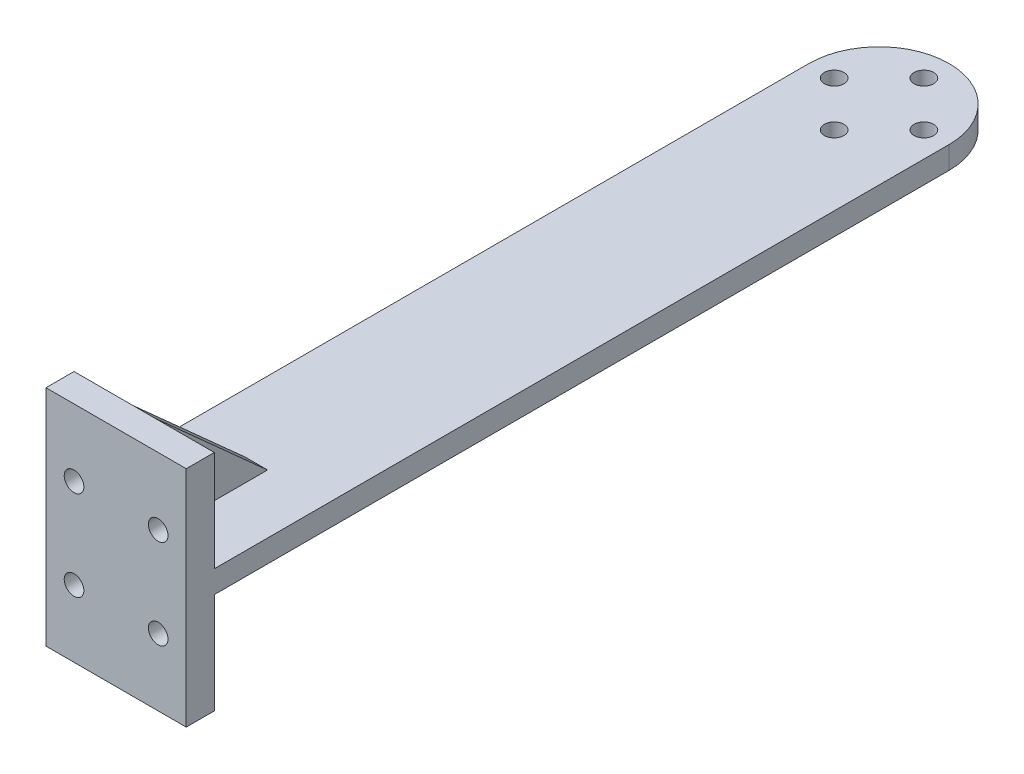
SolidWorks part; units mm, degrees
ref_plane "Front Plane" through (0, 0, 0) normal (0, 0, 1) x (1, 0, 0)
ref_plane "Top Plane" through (0, 0, 0) normal (0, 1, 0) x (1, 0, 0)
ref_plane "Right Plane" through (0, 0, 0) normal (1, 0, 0) x (0, 0, -1)
sketch "Sketch1" plane through (0, 0, 0) normal (0, 1, 0) x (1, 0, 0)
  line L1 (0, 0) -> (25, 0)
  line L2 (0, 0) -> (0, 136)
  line L4 (25, 0) -> (25, 136)
  arc A0 (25, 136) -> (0, 136) centre (12.5, 136) ccw
  point P6 (0, 0)
  point P7 (20, 136)
  point P8 (0, 0)
  dimension "D1" = 136
  dimension "D2" = 25
extrude "Boss-Extrude1" add sketch "Sketch1" along normal blind 4
sketch "Sketch2" plane through (0, 4, 0) normal (0, 1, 0) x (1, 0, 0)
  line L1 (0, 0) -> (25, 0)
  line L2 (0, 0) -> (0, 5)
  line L3 (0, 5) -> (25, 5)
  line L4 (25, 0) -> (25, 5)
  line L6 (0, 0) -> (25, 0) construction
  point P5 (-11.7073, 6.9513)
  point P6 (12.5, 0)
  point P8 (32.4044, 5)
  point P10 (12.5, 0)
  dimension "D1" = 5
  dimension "D2" = 25
extrude "Boss-Extrude2" add sketch "Sketch2" along normal blind 17.95
sketch "Sketch3" plane through (0, 0, -5) normal (0, 0, -1) x (-1, 0, 0)
  line L0 (-25, 2) -> (0, 2) construction
  line L1 (-25, 4) -> (-25, 0) construction
  line L2 (0, 4) -> (0, 0) construction
  line L3 (-25, 10) -> (0, 10) construction
  line L4 (-25, 21.95) -> (-25, 4) construction
  line L5 (0, 21.95) -> (0, 4) construction
  line L6 (-12.5, 2) -> (-12.5, 21.95) construction
  line L7 (-25, 21.95) -> (0, 21.95) construction
  circle A0 centre (-20, 10) radius 1.75
  circle A2 centre (-5, 10) radius 1.75
  dimension "D3" = 3.5
  dimension "D1" = 8
  dimension "D2" = 7.5
extrude "Cut-Extrude1" cut sketch "Sketch3" against normal through all
sketch "Sketch4" plane through (0, 0, -5) normal (0, 0, -1) x (-1, 0, 0)
  line L0 (-25, 21.95) -> (0, 21.95) construction
  line L1 (-14.5, 21.95) -> (-10.5, 21.95)
  line L2 (-14.5, 21.95) -> (-14.5, 4)
  line L3 (-14.5, 4) -> (-10.5, 4)
  line L4 (-10.5, 21.95) -> (-10.5, 4)
  line L5 (-25, 4) -> (0, 4) construction
  point P6 (-12.5, 4)
  point P9 (-12.5, 4)
  dimension "D1" = 4
extrude "Boss-Extrude3" add sketch "Sketch4" along normal blind 20
sketch "Sketch5" plane through (14.5, 0, 0) normal (1, 0, 0) x (0, 0, -1)
  line L0 (25, 4) -> (5, 21.95)
  line L1 (5, 21.95) -> (25, 21.95)
  line L2 (25, 21.95) -> (25, 4)
extrude "Cut-Extrude2" cut sketch "Sketch5" against normal through all
ref_plane "Plane1" through (0, 2, 0) normal (0, 1, 0) x (1, 0, 0)
mirror "Mirror1" about plane through (0, 2, 0) normal (0, 1, 0) of "Cut-Extrude2", "Boss-Extrude3", "Boss-Extrude2", "Cut-Extrude1"
sketch "Sketch6" plane through (0, 4, 0) normal (0, 1, 0) x (1, 0, 0)
  line L0 (12.5, 136) -> (12.5, 144) construction
  circle A0 centre (12.5, 136) radius 8 construction
  circle A1 centre (12.5, 144) radius 1.75
  circle A2 centre (20.5, 136) radius 1.75
  circle A3 centre (12.5, 128) radius 1.75
  circle A4 centre (4.5, 136) radius 1.75
  point P5 (1.5641, 126.9614)
  point P7 (12.5, 136)
  point P8 (12.7463, 144)
  point P15 (12.5, 136)
  dimension "D1" = 16
  dimension "D3" = 3.5
  dimension "D4" = 4
extrude "Cut-Extrude3" cut sketch "Sketch6" against normal through all
